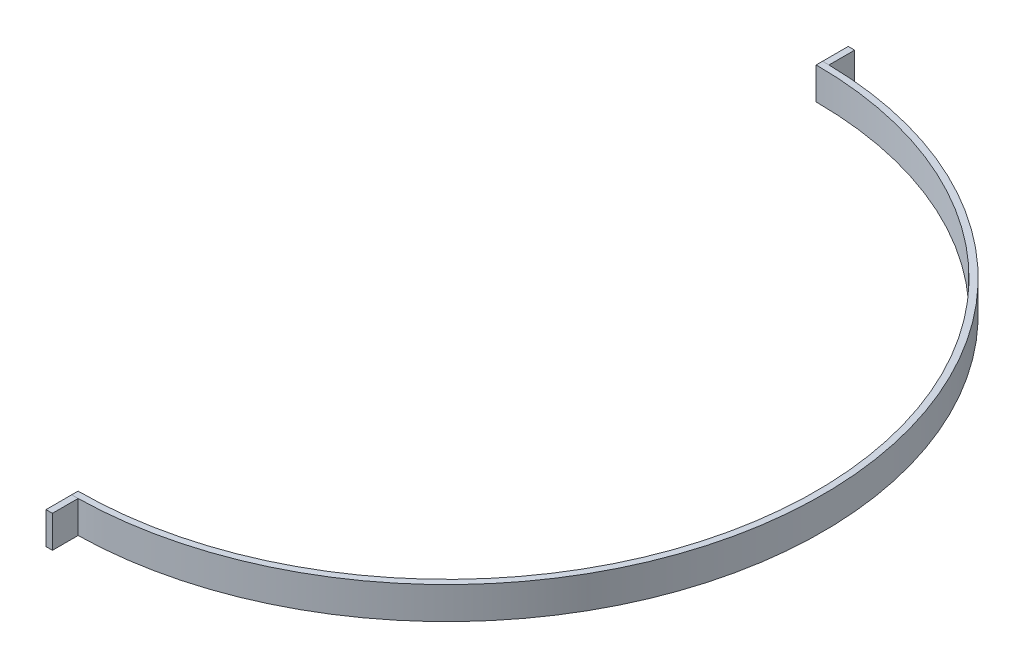
SolidWorks part; units mm, degrees
ref_plane "Front Plane" through (0, 0, 0) normal (0, 0, 1) x (1, 0, 0)
ref_plane "Top Plane" through (0, 0, 0) normal (0, 1, 0) x (1, 0, 0)
ref_plane "Right Plane" through (0, 0, 0) normal (1, 0, 0) x (0, 0, -1)
sketch "Sketch1" plane through (0, 0, 0) normal (0, 1, 0) x (1, 0, 0)
  line L0 (117, 0) -> (115, 0) construction
  line L1 (0, 117) -> (0, -117)
  line L2 (0, 117) -> (0, 124.9829)
  line L3 (0, 124.9829) -> (2, 124.9829)
  line L4 (2, 124.9829) -> (2, 116.9829)
  line L5 (2, 116.9829) -> (0, 117)
  line L6 (0, 0) -> (-215.0076, 0) construction
  line L7 (0, -124.9829) -> (2, -124.9829)
  line L8 (0, -117) -> (0, -124.9829)
  line L9 (2, -116.9829) -> (0, -117)
  line L10 (2, -124.9829) -> (2, -116.9829)
  circle A0 centre (0, 0) radius 115
  circle A1 centre (0, 0) radius 117
  dimension "D1" = 230
  dimension "D2" = 2
  dimension "D3" = 2
  dimension "D4" = 8
extrude "Boss-Extrude1" add sketch "Sketch1" along normal blind 10 contours L9 A1 L5 L1 A0 | A1 L8 L7 L10 | A1 L4 L3 L2
